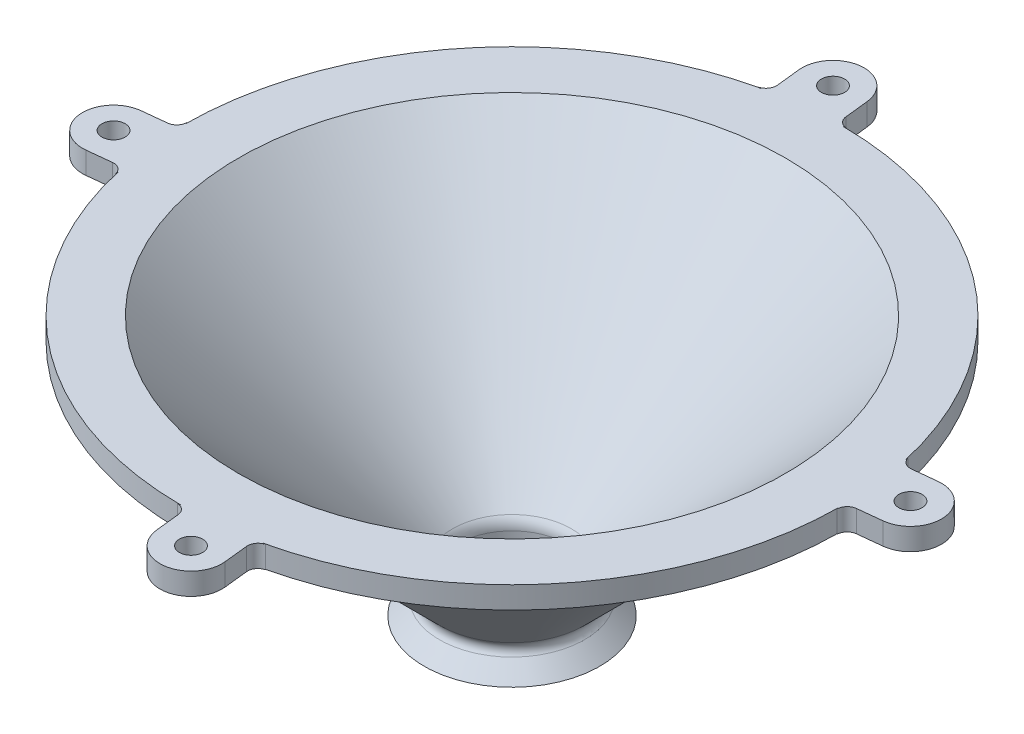
SolidWorks part; units mm, degrees
ref_plane "Front Plane" through (0, 0, 0) normal (0, 0, 1) x (1, 0, 0)
ref_plane "Top Plane" through (0, 0, 0) normal (0, 1, 0) x (1, 0, 0)
ref_plane "Right Plane" through (0, 0, 0) normal (1, 0, 0) x (0, 0, -1)
sketch "Sketch2" plane through (0, 0, 0) normal (1, 0, 0) x (0, 0, -1)
  line L5 (10.1, 0) -> (10.1, 6.9711)
  line L6 (10.1, 6.9711) -> (62.23, 59.1011)
  line L8 (64.3011, 54.1011) -> (15.1, 4.9)
  line L10 (62.23, 59.1011) -> (75, 59.1011)
  line L13 (0, 0) -> (0, 130.9762) construction
  line L14 (75, 59.1011) -> (75, 54.1011)
  line L15 (75, 54.1011) -> (64.3011, 54.1011)
  line L16 (15.1, 4.9) -> (20, 0)
  line L17 (20, 0) -> (10.1, 0)
  dimension "D1" = 5
  dimension "D2" = 75
  dimension "D3" = 10.1
  dimension "D4" = 20
  dimension "D5" = 45
  dimension "D6" = 5
  dimension "D9" = 5
  dimension "D10" = 45
  dimension "D11" = 62.23
revolve "Revolve1" add sketch "Sketch2" angle 360 about L13
fillet "Fillet1" radius 2 1 edges at (0, 4.9, -15.1)
fillet "Fillet2" radius 6 1 edges at (0, 6.9711, -10.1)
scale "Scale1" scale about centroid uniform scaling yes scale factor 0.85
sketch "Sketch4" plane through (0, 6.0324, 0) normal (0, -1, 0) x (1, 0, 0)
  circle A0 centre (0, 0) radius 10.6
  dimension "D1" = 21.2
extrude "Cut-Extrude2" cut sketch "Sketch4" against normal through all
sketch "Sketch9" plane through (0, 52.0183, 0) normal (0, -1, 0) x (1, 0, 0)
  line L0 (-62.1545, 14.4927) -> (-63.8149, -0.9321)
  line L1 (-0.9321, 63.8149) -> (14.4927, 62.1545)
  line L2 (63.8149, 0.9321) -> (62.1545, -14.4927)
  line L3 (-14.4927, -62.1545) -> (0.9321, -63.8149)
  line L8 (64.3163, -12.9583) -> (68.9557, -13.4577)
  line L9 (70.2401, -1.5267) -> (65.6007, -1.0272)
  line L10 (12.9583, 64.3163) -> (13.4577, 68.9557)
  line L11 (1.5267, 70.2401) -> (1.0272, 65.6007)
  line L12 (-64.3163, 12.9583) -> (-68.9557, 13.4577)
  line L13 (-70.2401, 1.5267) -> (-65.6007, 1.0272)
  line L14 (-12.9583, -64.3163) -> (-13.4577, -68.9557)
  line L15 (-1.5267, -70.2401) -> (-1.0272, -65.6007)
  line L16 (64.3163, -12.9583) -> (68.9557, -13.4577)
  line L17 (70.2401, -1.5267) -> (65.6007, -1.0272)
  line L18 (12.9583, 64.3163) -> (13.4577, 68.9557)
  line L19 (1.5267, 70.2401) -> (1.0272, 65.6007)
  line L20 (-64.3163, 12.9583) -> (-68.9557, 13.4577)
  line L21 (-70.2401, 1.5267) -> (-65.6007, 1.0272)
  line L22 (-12.9583, -64.3163) -> (-13.4577, -68.9557)
  line L23 (-1.5267, -70.2401) -> (-1.0272, -65.6007)
  circle A0 centre (-69.5979, 7.4922) radius 2.25 construction
  circle A1 centre (-7.4922, -69.5979) radius 2.25 construction
  circle A2 centre (69.5979, -7.4922) radius 2.25 construction
  circle A3 centre (7.4922, 69.5979) radius 2.25 construction
  circle A4 centre (-69.5979, 7.4922) radius 2.25
  circle A5 centre (-7.4922, -69.5979) radius 2.25
  circle A6 centre (69.5979, -7.4922) radius 2.25
  circle A7 centre (7.4922, 69.5979) radius 2.25
  arc A16 (0.9321, -63.8149) -> (62.1545, -14.4927) centre (0, 0) ccw
  arc A17 (64.3163, -12.9583) -> (62.1545, -14.4927) centre (64.1022, -14.9468) ccw
  arc A18 (68.9557, -13.4577) -> (70.2401, -1.5267) centre (69.5979, -7.4922) ccw
  arc A19 (63.8149, 0.9321) -> (65.6007, -1.0272) centre (65.8147, 0.9613) ccw
  arc A20 (63.8149, 0.9321) -> (14.4927, 62.1545) centre (0, 0) ccw
  arc A21 (12.9583, 64.3163) -> (14.4927, 62.1545) centre (14.9468, 64.1022) ccw
  arc A22 (13.4577, 68.9557) -> (1.5267, 70.2401) centre (7.4922, 69.5979) ccw
  arc A23 (-0.9321, 63.8149) -> (1.0272, 65.6007) centre (-0.9613, 65.8147) ccw
  arc A24 (-0.9321, 63.8149) -> (-62.1545, 14.4927) centre (0, 0) ccw
  arc A25 (-64.3163, 12.9583) -> (-62.1545, 14.4927) centre (-64.1022, 14.9468) ccw
  arc A26 (-68.9557, 13.4577) -> (-70.2401, 1.5267) centre (-69.5979, 7.4922) ccw
  arc A27 (-63.8149, -0.9321) -> (-65.6007, 1.0272) centre (-65.8147, -0.9613) ccw
  arc A28 (-63.8149, -0.9321) -> (-14.4927, -62.1545) centre (0, 0) ccw
  arc A29 (-12.9583, -64.3163) -> (-14.4927, -62.1545) centre (-14.9468, -64.1022) ccw
  arc A30 (-13.4577, -68.9557) -> (-1.5267, -70.2401) centre (-7.4922, -69.5979) ccw
  arc A31 (0.9321, -63.8149) -> (-1.0272, -65.6007) centre (0.9613, -65.8147) ccw
  arc A33 (64.3163, -12.9583) -> (62.1545, -14.4927) centre (64.1022, -14.9468) ccw
  arc A34 (68.9557, -13.4577) -> (70.2401, -1.5267) centre (69.5979, -7.4922) ccw
  arc A35 (63.8149, 0.9321) -> (65.6007, -1.0272) centre (65.8147, 0.9613) ccw
  arc A37 (12.9583, 64.3163) -> (14.4927, 62.1545) centre (14.9468, 64.1022) ccw
  arc A38 (13.4577, 68.9557) -> (1.5267, 70.2401) centre (7.4922, 69.5979) ccw
  arc A39 (-0.9321, 63.8149) -> (1.0272, 65.6007) centre (-0.9613, 65.8147) ccw
  arc A41 (-64.3163, 12.9583) -> (-62.1545, 14.4927) centre (-64.1022, 14.9468) ccw
  arc A42 (-68.9557, 13.4577) -> (-70.2401, 1.5267) centre (-69.5979, 7.4922) ccw
  arc A43 (-63.8149, -0.9321) -> (-65.6007, 1.0272) centre (-65.8147, -0.9613) ccw
  arc A45 (-12.9583, -64.3163) -> (-14.4927, -62.1545) centre (-14.9468, -64.1022) ccw
  arc A46 (-13.4577, -68.9557) -> (-1.5267, -70.2401) centre (-7.4922, -69.5979) ccw
  arc A47 (0.9321, -63.8149) -> (-1.0272, -65.6007) centre (0.9613, -65.8147) ccw
  dimension "D1" = 0
extrude "Boss-Extrude1" add sketch "Sketch9" against normal up to surface (4.25 mm away) up to face at (0, 56.2683, -52.8955)
fillet "Fillet4" radius 3 2 edges at (0, 13.9728, 10.6) (0, 52.0183, -54.6559)
